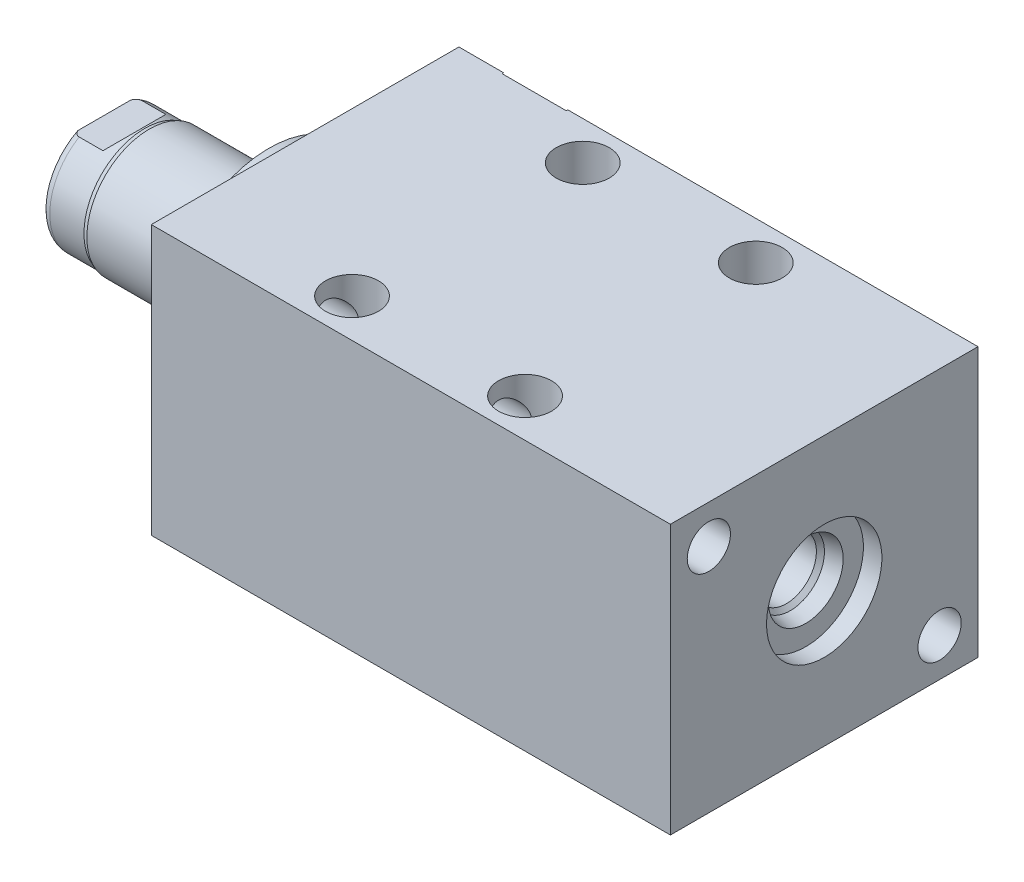
SolidWorks part; units mm, degrees
material "Alloy Steel"
ref_plane "Front Plane" through (0, 0, 0) normal (0, 0, 1) x (1, 0, 0)
ref_plane "Top Plane" through (0, 0, 0) normal (0, 1, 0) x (1, 0, 0)
ref_plane "Right Plane" through (0, 0, 0) normal (1, 0, 0) x (0, 0, -1)
ref_plane "Plane1" through (0, 0, 0) normal (1, 0, 0) x (0, 0, -1)
sketch "Sketch1" plane through (0, 0, 0) normal (1, 0, 0) x (0, 0, -1)
  line L0 (-25.4, 22.225) -> (25.4, 22.225)
  line L1 (25.4, 22.225) -> (25.4, -22.225)
  line L2 (25.4, -22.225) -> (-25.4, -22.225)
  line L3 (-25.4, -22.225) -> (-25.4, 22.225)
  line L4 (0, -24.4475) -> (0, 24.4475) construction
  dimension "D1" = 44.45
  dimension "D2" = 22.225
  dimension "D3" = 50.8
extrude "Extrude1" add sketch "Sketch1" along normal blind 85.725
ref_plane "Plane12" through (0, 14.3002, 0) normal (0, 1, 0) x (-1, 0, 0)
sketch "S2D0002" plane through (0, 14.3002, 0) normal (0, 1, 0) x (-1, 0, 0)
  line L0 (-18.8849, -25.146) -> (-22.225, -25.146)
  line L1 (-18.8849, -25.146) -> (-18.3423, -22.5933)
  line L2 (-18.3423, -22.5933) -> (-17.6784, -21.9294)
  line L3 (-17.6784, -21.9294) -> (-17.6784, -11.176)
  line L4 (-17.6784, -11.176) -> (-12.7, -11.176)
  line L5 (-12.7, -11.176) -> (-12.7, -25.4)
  line L6 (-12.7, -19.1384) -> (-12.7, 0.6985) construction
  line L7 (0, -25.4) -> (0, 25.4) construction
  line L8 (-22.225, -25.4) -> (-22.225, -25.146)
  line L9 (-85.725, -25.4) -> (0, -25.4) construction
  line L10 (-22.225, -25.4) -> (-12.7, -25.4)
  dimension "D1" = 14.224
  dimension "D2" = 12.7
  dimension "D3" = 9.9568
  dimension "D4" = 45
  dimension "D5" = 12.3698
  dimension "D6" = 12
  dimension "D7" = 2.5527
  dimension "D8" = 0.254
  dimension "D9" = 19.05
revolve "Cut-Revolve1" cut sketch "S2D0002" angle 360 about L6
ref_plane "Plane3" through (41.148, 0, -25.146) normal (0, 1, 0) x (1, 0, 0)
sketch "Sketch3" plane through (41.148, 0, -25.146) normal (0, 1, 0) x (1, 0, 0)
  line L0 (34.8869, 0) -> (38.227, 0)
  line L1 (34.8869, 0) -> (34.3443, -2.5527)
  line L2 (34.3443, -2.5527) -> (33.6804, -3.2166)
  line L3 (33.6804, -3.2166) -> (33.6804, -13.97)
  line L4 (33.6804, -13.97) -> (28.702, -13.97)
  line L5 (28.702, -13.97) -> (28.702, 0.254)
  line L6 (28.702, -21.9564) -> (28.702, 0.6985) construction
  line L7 (-41.148, 0.254) -> (-41.148, -50.546) construction
  line L8 (38.227, 0.254) -> (38.227, 0)
  line L9 (44.577, 0.254) -> (-23.1638, 0.254) construction
  line L10 (38.227, 0.254) -> (28.702, 0.254)
  dimension "D1" = 14.224
  dimension "D2" = 69.85
  dimension "D3" = 9.9568
  dimension "D4" = 45
  dimension "D5" = 12
  dimension "D6" = 12.3698
  dimension "D7" = 2.5527
  dimension "D8" = 0.254
  dimension "D9" = 19.05
revolve "Cut-Revolve2" cut sketch "Sketch3" angle 360 about L6
ref_plane "Plane4" through (53.975, 0, 0) normal (0, 0, 1) x (0, -1, 0)
sketch "Sketch4" plane through (53.975, 0, 0) normal (0, 0, 1) x (0, -1, 0)
  line L0 (6.1849, 28.702) -> (9.525, 28.702)
  line L1 (6.1849, 28.702) -> (5.6423, 26.1493)
  line L2 (5.6423, 26.1493) -> (4.9784, 25.4854)
  line L3 (4.9784, 25.4854) -> (4.9784, 17.3482)
  line L4 (4.9784, 17.3482) -> (0, 17.3482)
  line L5 (0, 17.3482) -> (0, 31.75)
  line L6 (0, -15.0954) -> (0, 0.5677) construction
  line L7 (0, 31.75) -> (9.525, 31.75)
  line L9 (-22.225, 31.75) -> (22.225, 31.75) construction
  line L10 (9.525, 31.75) -> (9.525, 28.702)
  dimension "D1" = 11.3538
  dimension "D2" = 9.9568
  dimension "D3" = 3.048
  dimension "D4" = 19.05
  dimension "D5" = 2.5527
  dimension "D6" = 12
  dimension "D7" = 45
  dimension "D8" = 12.3698
revolve "Cut-Revolve3" cut sketch "Sketch4" angle 360 about L6
sketch "Sketch5" plane through (0, 0, 0) normal (-1, 0, 0) x (0, 0, 1)
  circle A0 centre (0, 0) radius 17.4625
  dimension "D1" = 34.925
extrude "Extrude2" add sketch "Sketch5" along normal blind 5.969
ref_plane "Plane5" through (0, 0, 0) normal (0, -1, 0) x (0, 0, 1)
sketch "Sketch6" plane through (0, 0, 0) normal (0, -1, 0) x (0, 0, 1)
  line L0 (0, 5.969) -> (-10.3187, 5.969)
  line L1 (-10.3187, 5.969) -> (-10.3187, 33.147)
  line L2 (-10.3187, 33.147) -> (0, 33.147)
  line L3 (0, 33.147) -> (0, 5.969)
  line L4 (0, -5.7546) -> (0, 21.1709) construction
  line L5 (17.4625, 5.969) -> (-17.4625, 5.969) construction
  line L6 (25.4, -85.725) -> (-25.4, -85.725) construction
  dimension "D1" = 118.872
  dimension "D2" = 20.6375
revolve "Revolve1" add sketch "Sketch6" angle 360 about L4
ref_plane "Plane6" through (-18.5113, 3.2639, 0) normal (0, 0, 1) x (0, 1, 0)
sketch "S2D0001" plane through (-18.5113, 3.2639, 0) normal (0, 0, 1) x (0, 1, 0)
  line L0 (0, 12.7) -> (0, -0.2995)
  line L1 (0, -0.2995) -> (-3.2639, -0.2995)
  line L2 (1.1176, 14.6357) -> (-3.2639, 14.6357)
  line L3 (-3.2639, 14.6357) -> (-3.2639, -0.2995)
  line L4 (0, 12.7) -> (1.1176, 14.6357)
  line L5 (-3.2639, -18.5113) -> (-3.2639, 2.765) construction
  line L6 (7.0549, 14.6357) -> (-13.5826, 14.6357) construction
  dimension "D1" = 30
  dimension "D2" = 8.763
  dimension "D3" = 6.5278
  dimension "D4" = 14.9352
revolve "Cut-Revolve4" cut sketch "S2D0001" angle 360 about L5
ref_plane "Plane7" through (0, 0, 0) normal (0, 1, 0) x (0, 0, -1)
sketch "Sketch8" plane through (0, 0, 0) normal (0, 1, 0) x (0, 0, -1)
  line L0 (-10.3187, 25.7302) -> (-10.033, 26.4922)
  line L1 (-10.033, 26.4922) -> (-10.033, 32.131)
  line L2 (0, 12.6594) -> (0, 20.8178) construction
  line L3 (-10.3187, 25.7302) -> (-10.3187, 33.147)
  line L4 (-9.6449, 33.147) -> (-10.3187, 33.147)
  line L5 (10.3187, 33.147) -> (-10.3187, 33.147) construction
  line L6 (-10.3187, 33.147) -> (-10.3187, 5.969) construction
  arc A0 (-9.6449, 33.147) -> (-10.033, 32.131) centre (-8.509, 32.131) ccw
  dimension "D2" = 1.524
  dimension "D1" = 20.066
  dimension "D3" = 1.016
  dimension "D4" = 0.762
  dimension "D5" = 6.6548
revolve "Cut-Revolve5" cut sketch "Sketch8" angle 360 about L2
ref_plane "Plane11" through (0, 0, 0) normal (0, 0, -1) x (0, -1, 0)
sketch "Sketch12" plane through (0, 0, 0) normal (0, 0, -1) x (0, -1, 0)
  line L0 (8.5852, 33.147) -> (8.5852, 28.194)
  line L1 (8.5852, 28.194) -> (10.033, 26.7462)
  line L2 (-8.5852, 33.147) -> (-8.5852, 28.194)
  line L3 (-8.5852, 28.194) -> (-10.033, 26.7462)
  line L4 (8.5852, 33.147) -> (10.033, 33.147)
  line L5 (0, 13.7262) -> (0, 20.767) construction
  line L6 (-10.033, 26.7462) -> (-10.033, 33.147)
  line L7 (9.6449, 33.147) -> (-9.6449, 33.147) construction
  line L8 (10.033, 26.4922) -> (10.033, 32.131) construction
  line L9 (10.033, 26.7462) -> (10.033, 33.147)
  line L10 (-8.5852, 33.147) -> (-10.033, 33.147)
  dimension "D1" = 17.1704
  dimension "D2" = 4.953
  dimension "D3" = 45
extrude "Cut-Extrude4" cut sketch "Sketch12" against normal mid plane 60.96
hole_wizard "Hole1" positions "Sketch15" profile "Sketch14" legacy end condition up to next
sketch "Sketch15" plane through (0, 0, 0) normal (-1, 0, 0) x (0, 0, 1)
  line L0 (0, 0) -> (-29.9914, 0) construction
  line L1 (0, 0) -> (0, 25.7648) construction
  point P0 (-19.05, -15.875)
  point P11 (19.05, 15.875)
  dimension "D1" = 15.875
  dimension "D2" = 19.05
  dimension "D3" = 31.75
  dimension "D4" = 38.1
sketch "Sketch14" plane through (0, -15.875, -19.05) normal (0, 1, 0) x (0, 0, 1)
  line L0 (0, 0) -> (0, 85.725)
  line L1 (0, 85.725) -> (3.5687, 85.725)
  line L2 (3.5687, 85.725) -> (3.5687, 0)
  line L3 (3.5687, 0) -> (0, 0)
  line L4 (0, 110) -> (0, -10) construction
  dimension "Diameter" = 7.1374
  dimension "Depth" = 85.725
hole_wizard "Hole2" positions "Sketch17" profile "Sketch16" legacy
sketch "Sketch17" plane through (0, 22.225, 0) normal (0, 1, 0) x (-1, 0, 0)
  line L0 (0, 0) -> (-59.3363, 0) construction
  line L1 (0, -25.4) -> (0, 25.4) construction
  point P0 (-26.797, -19.05)
  point P9 (-26.797, 19.05)
  dimension "D1" = 38.1
  dimension "D2" = 26.797
sketch "Sketch16" plane through (26.797, 22.225, -19.05) normal (1, 0, 0) x (0, 0, 1)
  line L0 (0, 0) -> (0, 44.45)
  line L1 (0, 44.45) -> (4.3688, 44.45)
  line L2 (4.3688, 44.45) -> (4.3688, 0)
  line L3 (4.3688, 0) -> (0, 0)
  line L4 (0, 110) -> (0, -10) construction
  dimension "Diameter" = 8.7376
  dimension "Depth" = 44.45
pattern_linear "LPattern1" count 2 spacing 28.575 along (1, 0, 0) of "Hole2"
